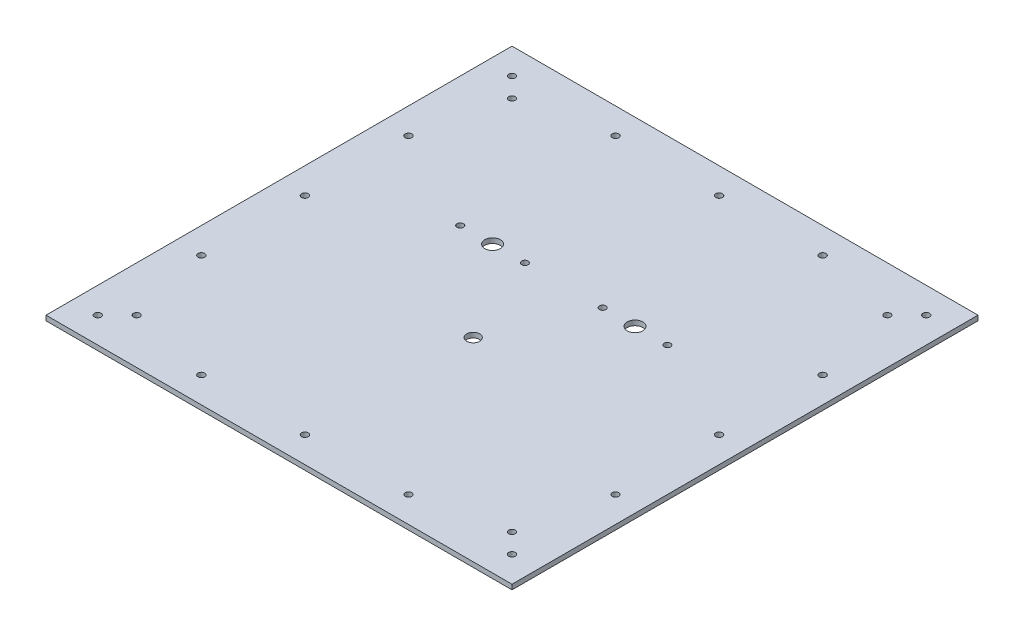
SolidWorks part; units mm, degrees
material "6061 Alloy"
ref_plane "Front Plane" through (0, 0, 0) normal (0, 0, 1) x (1, 0, 0)
ref_plane "Top Plane" through (0, 0, 0) normal (0, 1, 0) x (1, 0, 0)
ref_plane "Right Plane" through (0, 0, 0) normal (1, 0, 0) x (0, 0, -1)
sketch "Sketch1" plane through (0, 0, 0) normal (0, 1, 0) x (1, 0, 0)
  line L1 (-228.6, -228.6) -> (228.6, -228.6)
  line L2 (-228.6, -228.6) -> (-228.6, 228.6)
  line L3 (-228.6, 228.6) -> (228.6, 228.6)
  line L4 (228.6, -228.6) -> (228.6, 228.6)
  line L5 (-228.6, -228.6) -> (228.6, 228.6) construction
  line L6 (-228.6, 228.6) -> (228.6, -228.6) construction
  point P0 (0, 0)
  dimension "D1" = 457.2
  dimension "D2" = 457.2
extrude "Boss-Extrude1" add sketch "Sketch1" along normal blind 4.826
sketch "Sketch2" plane through (0, 4.826, 0) normal (0, 1, 0) x (1, 0, 0)
  line L0 (-228.6, 0) -> (228.6, 0)
  line L1 (-228.6, 228.6) -> (-228.6, -228.6) construction
  line L2 (228.6, -228.6) -> (228.6, 228.6) construction
  line L3 (0, 228.6) -> (0, -228.6)
  line L4 (228.6, 228.6) -> (-228.6, 228.6) construction
  line L5 (-228.6, -228.6) -> (228.6, -228.6) construction
  circle A0 centre (69.85, 50.8) radius 7.62
  circle A1 centre (-69.85, 50.8) radius 7.62
  circle A2 centre (0, -38.1) radius 6.35
  circle A3 centre (-38.1, 50.8) radius 3.175
  circle A4 centre (-101.6, 50.8) radius 3.175
  circle A5 centre (38.1, 50.8) radius 3.175
  circle A6 centre (101.6, 50.8) radius 3.175
  dimension "D1" = 15.24
  dimension "D2" = 15.24
  dimension "D3" = 12.7
  dimension "D4" = 88.9
  dimension "D6" = 88.9
  dimension "D7" = 139.7
  dimension "D8" = 69.85
  dimension "D9" = 31.75
  dimension "D10" = 63.5
  dimension "D11" = 6.35
  dimension "D12" = 6.35
  dimension "D13" = 31.75
  dimension "D14" = 63.5
  dimension "D15" = 6.35
  dimension "D16" = 6.35
  dimension "D5" = 38.1
extrude "Cut-Extrude1" cut sketch "Sketch2" against normal blind 25.4 contours A0 | A1 | A2
sketch "Sketch4" plane through (0, 4.826, 0) normal (0, 1, 0) x (1, 0, 0)
  line L0 (-228.6, 228.6) -> (-228.6, -228.6) construction
  line L1 (-228.6, -228.6) -> (228.6, -228.6) construction
  line L2 (228.6, -228.6) -> (228.6, 228.6) construction
  line L3 (228.6, 228.6) -> (-228.6, 228.6) construction
  circle A0 centre (-184.15, 184.15) radius 3.175
  circle A1 centre (184.15, 184.15) radius 3.175
  circle A2 centre (184.15, -184.15) radius 3.175
  circle A3 centre (-184.15, -184.15) radius 3.175
  dimension "D1" = 6.35
  dimension "D2" = 6.35
  dimension "D3" = 6.35
  dimension "D4" = 6.35
  dimension "D5" = 44.45
  dimension "D7" = 44.45
  dimension "D8" = 44.45
  dimension "D9" = 44.45
  dimension "D10" = 44.45
  dimension "D11" = 44.45
  dimension "D6" = 44.45
  dimension "D12" = 44.45
extrude "Cut-Extrude2" cut sketch "Sketch4" against normal blind 5.08
sketch "Sketch6" plane through (0, 4.826, 0) normal (0, 1, 0) x (1, 0, 0)
  line L0 (228.6, 228.6) -> (-228.6, 228.6) construction
  line L1 (-228.6, 228.6) -> (-228.6, -228.6) construction
  line L2 (-228.6, -228.6) -> (228.6, -228.6) construction
  line L3 (228.6, -228.6) -> (228.6, 228.6) construction
  circle A0 centre (203.2, -203.2) radius 3.2639
  circle A1 centre (-203.2, 203.2) radius 3.2639
  circle A2 centre (203.2, -101.6) radius 3.2639
  circle A3 centre (203.2, 0) radius 3.2639
  circle A4 centre (203.2, 101.6) radius 3.2639
  circle A5 centre (203.2, 203.2) radius 3.2639
  circle A6 centre (101.6, -203.2) radius 3.2639
  circle A7 centre (0, -203.2) radius 3.2639
  circle A8 centre (-101.6, -203.2) radius 3.2639
  circle A9 centre (-203.2, -203.2) radius 3.2639
  circle A10 centre (304.8, -203.2) radius 3.2639
  circle A11 centre (-101.6, 203.2) radius 3.2639
  circle A12 centre (406.4, -203.2) radius 3.2639
  circle A13 centre (0, 203.2) radius 3.2639
  circle A14 centre (508, -203.2) radius 3.2639
  circle A15 centre (101.6, 203.2) radius 3.2639
  circle A16 centre (203.2, -304.8) radius 3.2639
  circle A17 centre (-203.2, 101.6) radius 3.2639
  circle A18 centre (203.2, -406.4) radius 3.2639
  circle A19 centre (-203.2, 0) radius 3.2639
  circle A20 centre (203.2, -508) radius 3.2639
  circle A21 centre (-203.2, -101.6) radius 3.2639
  dimension "D1" = 6.5278
  dimension "D2" = 6.5278
  dimension "D3" = 25.4
  dimension "D5" = 25.4
  dimension "D6" = 25.4
  dimension "D4" = 25.4
  dimension "D7" = 5
  dimension "D8" = 5
  dimension "D9" = 4
  dimension "D10" = 4
extrude "Cut-Extrude3" cut sketch "Sketch6" against normal blind 12.7
ref_point "Point2"
ref_point "Point1"
sketch "Sketch8" plane through (0, 4.826, 0) normal (0, 1, 0) x (1, 0, 0)
  circle A0 centre (-101.6, 50.8) radius 3.175
  circle A1 centre (-38.1, 50.8) radius 3.175
  circle A2 centre (38.1, 50.8) radius 3.175
  circle A3 centre (101.6, 50.8) radius 3.175
  circle A4 centre (69.85, 50.8) radius 7.62 construction
  circle A5 centre (-69.85, 50.8) radius 7.62 construction
  dimension "D1" = 63.5
  dimension "D2" = 31.75
  dimension "D3" = 63.5
  dimension "D4" = 31.75
  dimension "D5" = 6.35
  dimension "D6" = 6.35
  dimension "D7" = 6.35
  dimension "D8" = 6.35
extrude "Cut-Extrude5" cut sketch "Sketch8" against normal through all
